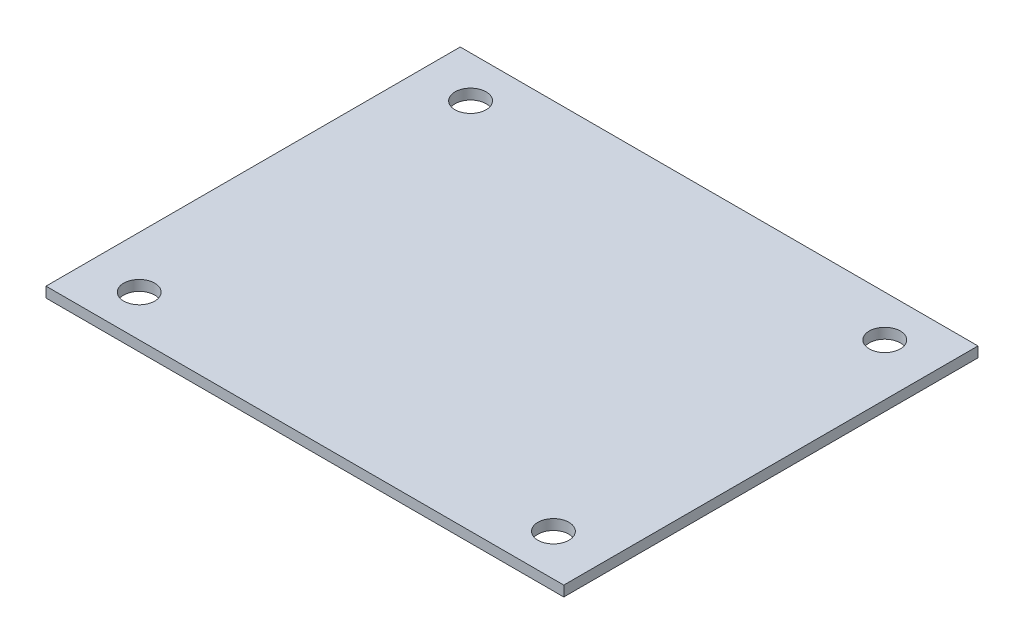
SolidWorks part; units mm, degrees
material "Custom Plastic"
ref_plane "Front Plane" through (0, 0, 0) normal (0, 0, 1) x (1, 0, 0)
ref_plane "Top Plane" through (0, 0, 0) normal (0, 1, 0) x (1, 0, 0)
ref_plane "Right Plane" through (0, 0, 0) normal (1, 0, 0) x (0, 0, -1)
sketch "Sketch1" plane through (0, 0, 0) normal (0, 1, 0) x (1, 0, 0)
  line L0 (-55, 0) -> (55, 0) construction
  line L1 (-25, 20) -> (25, 20)
  line L2 (-25, 20) -> (-25, -20)
  line L3 (-25, -20) -> (25, -20)
  line L4 (25, 20) -> (25, -20)
  line L5 (-25, 20) -> (25, -20) construction
  line L6 (-25, -20) -> (25, 20) construction
  line L7 (0, -55) -> (0, 55) construction
  circle A3 centre (-20, -16) radius 1.5
  circle A4 centre (-20, 16) radius 1.5
  circle A5 centre (20, -16) radius 1.5
  circle A6 centre (20, 16) radius 1.5
  point P1 (0, 0)
  dimension "D3" = 20
  dimension "D6" = 3
  dimension "D1" = 40
  dimension "D2" = 50
extrude "Boss-Extrude1" add sketch "Sketch1" along normal blind 1
